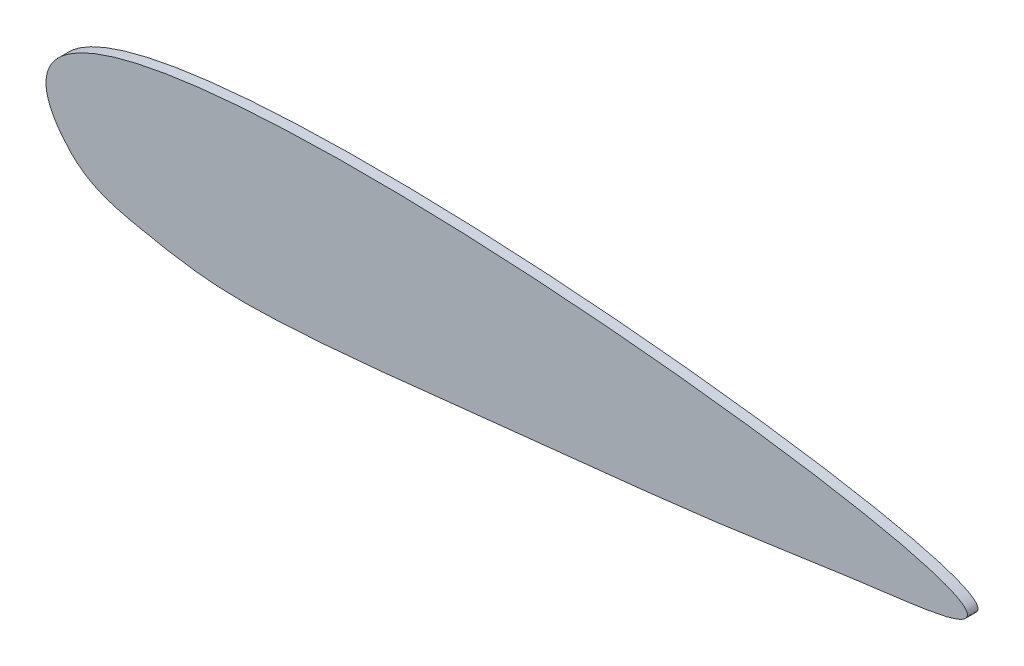
SolidWorks part; units mm, degrees
material "ﾊﾞﾙｻ"
ref_plane "正面" through (0, 0, 0) normal (0, 0, 1) x (1, 0, 0)
ref_plane "平面" through (0, 0, 0) normal (0, 1, 0) x (1, 0, 0)
ref_plane "右側面" through (0, 0, 0) normal (1, 0, 0) x (0, 0, -1)
sketch "ｽｹｯﾁ1" plane through (0, 0, 0) normal (0, 0, 1) x (1, 0, 0)
  spline S0 degree 3 poles (341.1277, 16.7682) (-57.661, 63.7481) (7.6076, -8.7263) (23.0443, -12.2292) (42.7966, -15.806) (75.8096, -14.8872) (125.0532, -8.8253) (181.6352, -3.5635) (222.0514, 2.9804) (341.1277, 16.7682) (-57.661, 63.7481) (7.6076, -8.7263) knots -0.612829 -0.536011 -0.495122 0 0.014045 0.052533 0.090256 0.134135 0.247127 0.387171 0.463989 0.504878 1 1.014045 1.052533 1.090256 only from (0, 0) to (0, 0)
  dimension "D1" = 250
extrude "ﾎﾞｽ - 押し出し1" add sketch "ｽｹｯﾁ1" along normal blind 3
